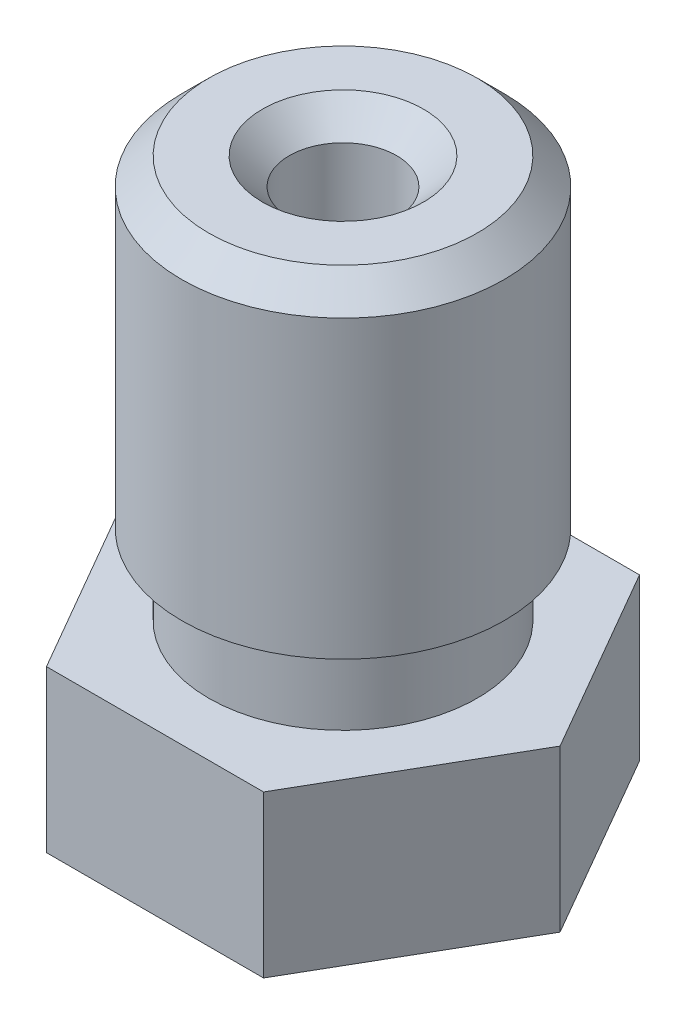
SolidWorks part; units mm, degrees
ref_plane "Front Plane" through (0, 0, 0) normal (0, 0, 1) x (1, 0, 0)
ref_plane "Top Plane" through (0, 0, 0) normal (0, 1, 0) x (1, 0, 0)
ref_plane "Right Plane" through (0, 0, 0) normal (1, 0, 0) x (0, 0, -1)
ref_plane "Plane1" through (0, 0, 0) normal (0, -1, 0) x (1, 0, 0)
sketch "Sketch1" plane through (0, 0, 0) normal (0, -1, 0) x (1, 0, 0)
  line L0 (2.0207, -3.5) -> (4.0415, 0)
  line L1 (4.0415, 0) -> (2.0207, 3.5)
  line L2 (2.0207, 3.5) -> (-2.0207, 3.5)
  line L3 (-2.0207, 3.5) -> (-4.0415, 0)
  line L4 (-4.0415, 0) -> (-2.0207, -3.5)
  line L5 (-2.0207, -3.5) -> (2.0207, -3.5)
extrude "Boss-Extrude1" add sketch "Sketch1" against normal blind 3
ref_plane "Plane2" through (0, 0, 0) normal (0, 0, -1) x (-1, 0, 0)
sketch "Sketch2" plane through (0, 0, 0) normal (0, 0, -1) x (-1, 0, 0)
  line L0 (-2.5, 3) -> (0, 3)
  line L1 (0, 3) -> (0, 10.5)
  line L2 (0, 10.5) -> (-3, 10.5)
  line L3 (-3, 10.5) -> (-3, 4.5)
  line L4 (-3, 4.5) -> (-2.5, 4.5)
  line L5 (-2.5, 4.5) -> (-2.5, 3)
  line L6 (0, 3) -> (0, 10.5) construction
revolve "Revolve1" add sketch "Sketch2" angle 360 about L6
sketch "Sketch3" plane through (0, 0, 0) normal (0, 0, 1) x (1, 0, 0)
  line L0 (2.5, 0) -> (0, 0)
  line L1 (0, 0) -> (0, -2)
  line L2 (0, -2) -> (0.5, -2)
  line L3 (0.5, -2) -> (2.5, 0)
  line L4 (0, 0) -> (0, -2) construction
revolve "Revolve2" add sketch "Sketch3" angle 360 about L4
sketch "Sketch4" plane through (0, 0, 0) normal (0, 0, -1) x (-1, 0, 0)
  line L0 (-0.2, -2) -> (0, -2)
  line L1 (0, -2) -> (0, 10.5)
  line L2 (0, 10.5) -> (-1, 10.5)
  line L3 (-1, 10.5) -> (-1, 0)
  line L4 (-1, 0) -> (-0.75, -0.2273)
  line L5 (-0.75, -0.2273) -> (-0.75, -0.7)
  line L6 (-0.75, -0.7) -> (-0.2, -1.2)
  line L7 (-0.2, -1.2) -> (-0.2, -2)
  line L8 (0, -2) -> (0, 10.5) construction
revolve "Cut-Revolve1" cut sketch "Sketch4" angle 360 about L8
chamfer "Chamfer1" distance 0.5 angle 45 2 edges at (0, 10.5, 3) (0, 10.5, 1)
